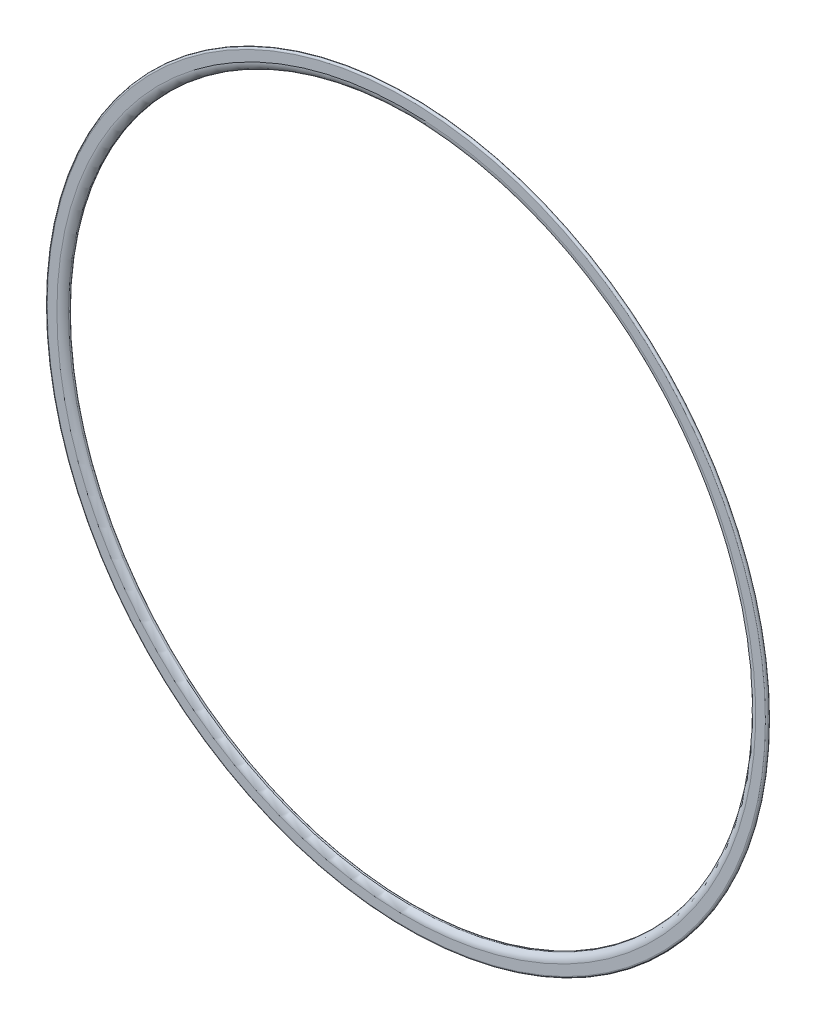
SolidWorks part; units mm, degrees
material "PBT General Purpose"
ref_plane "Front Plane" through (0, 0, 0) normal (0, 0, 1) x (1, 0, 0)
ref_plane "Top Plane" through (0, 0, 0) normal (0, 1, 0) x (1, 0, 0)
ref_plane "Right Plane" through (0, 0, 0) normal (1, 0, 0) x (0, 0, -1)
sketch "Sketch1" plane through (0, 0, 0) normal (1, 0, 0) x (0, 0, -1)
  line L0 (0, 105) -> (0, 102.1651) construction
  line L1 (0.5, 105) -> (0.5, 102.1651)
  line L2 (-0.5, 105) -> (-0.5, 102.1651)
  line L3 (0, 0) -> (-13.9406, 0) construction
  arc A0 (0, 102.1651) -> (1, 100.433) centre (2, 102.1651) ccw construction
  arc A1 (0.5, 102.1651) -> (1.25, 100.866) centre (2, 102.1651) ccw
  arc A2 (-0.5, 102.1651) -> (0.75, 100) centre (2, 102.1651) ccw
  arc A3 (0.5, 105) -> (-0.5, 105) centre (0, 105) ccw
  arc A4 (1.25, 100.866) -> (0.75, 100) centre (1, 100.433) cw
  dimension "D5" = 2
  dimension "D6" = 60
  dimension "D3" = 100
  dimension "D4" = 210
  dimension "D1" = 0.5
  dimension "D2" = 0.5
revolve "Revolve2" add sketch "Sketch1" angle 360 about L3
